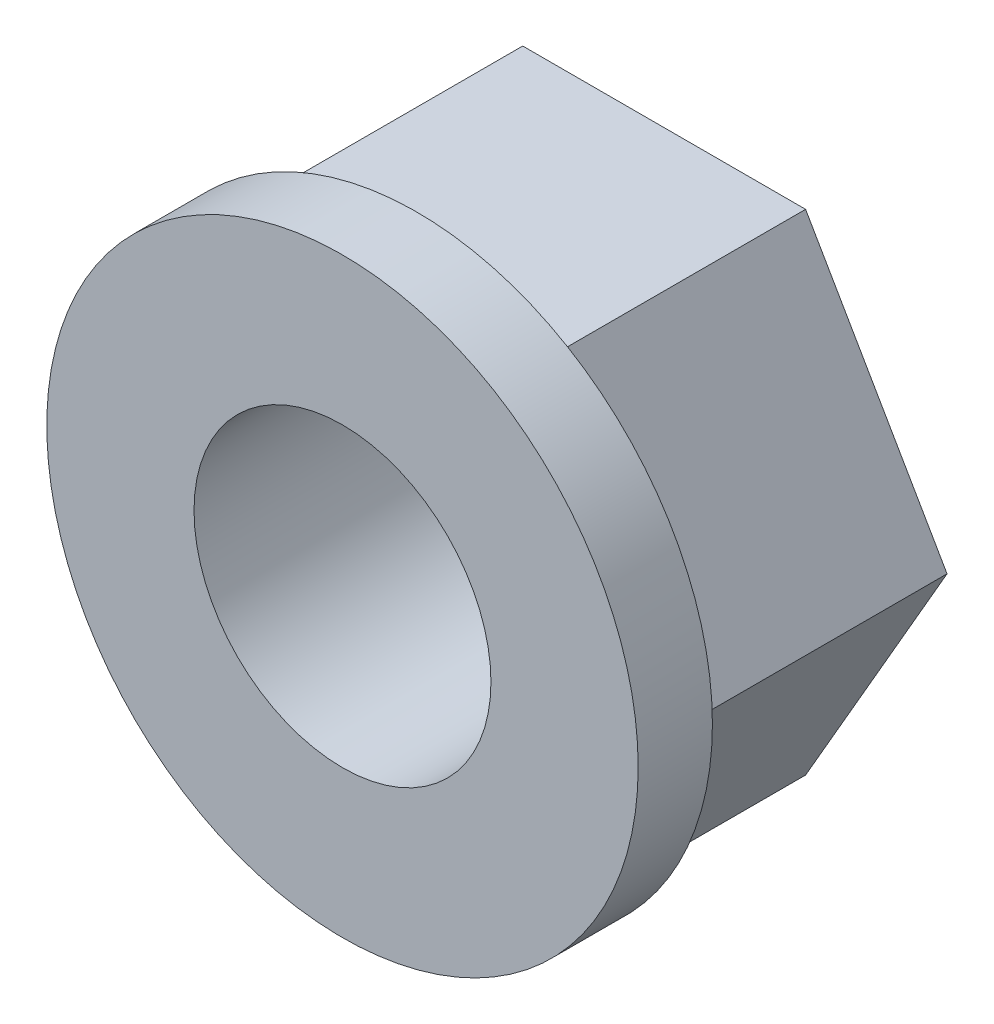
SolidWorks part; units mm, degrees
ref_plane "Front Plane" through (0, 0, 0) normal (0, 0, 1) x (1, 0, 0)
ref_plane "Top Plane" through (0, 0, 0) normal (0, 1, 0) x (1, 0, 0)
ref_plane "Right Plane" through (0, 0, 0) normal (1, 0, 0) x (0, 0, -1)
sketch "Sketch1" plane through (0, 0, 0) normal (0, 0, 1) x (1, 0, 0)
  line L1 (-5.7158, 0) -> (-2.8579, -4.95)
  line L2 (-2.8579, -4.95) -> (2.8579, -4.95)
  line L3 (2.8579, -4.95) -> (5.7158, 0)
  line L4 (5.7158, 0) -> (2.8579, 4.95)
  line L5 (2.8579, 4.95) -> (-2.8579, 4.95)
  line L6 (-2.8579, 4.95) -> (-5.7158, 0)
  circle A0 centre (0, 0) radius 4.95 construction
  circle A1 centre (0, 0) radius 3
  dimension "D2" = 6
  dimension "D1" = 9.9
extrude "Boss-Extrude1" add sketch "Sketch1" along normal blind 5
sketch "Sketch2" plane through (0, 0, 5) normal (0, 0, 1) x (1, 0, 0)
  circle A0 centre (0, 0) radius 5.975
  circle A1 centre (0, 0) radius 3
  dimension "D1" = 11.95
extrude "Boss-Extrude2" add sketch "Sketch2" along normal blind 1.5
